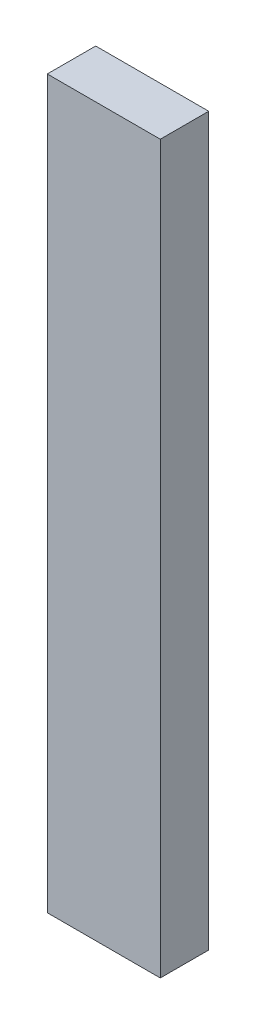
SolidWorks part; units mm, degrees
ref_plane "Front Plane" through (0, 0, 0) normal (1, 0, 0) x (0, 1, 0)
ref_plane "Top Plane" through (0, 0, 0) normal (0, 0, 1) x (0, 1, 0)
ref_plane "Right Plane" through (0, 0, 0) normal (0, 1, 0) x (-1, 0, 0)
sketch "Sketch1" plane through (0, 0, 0) normal (0, 0, 1) x (0, 1, 0)
  line L5 (0, 0) -> (57.15, 0)
  line L6 (0, 0) -> (0, 8.89)
  line L7 (0, 8.89) -> (57.15, 8.89)
  line L8 (57.15, 0) -> (57.15, 8.89)
  dimension "D1" = 8.89
  dimension "D2" = 57.15
extrude "Boss-Extrude1" add sketch "Sketch1" along normal blind 3.81
ref_plane "Plane1" through (-4.445, 0, 0) normal (1, 0, 0) x (0, 1, 0)
sketch "Sketch2" plane through (-4.445, 0, 0) normal (1, 0, 0) x (0, 1, 0)
  line L0 (5.2423, 8.1921) -> (5.2423, 3.81)
  line L1 (0, 3.81) -> (57.15, 3.81) construction
  line L2 (5.2423, 3.81) -> (0, 3.81)
  arc A0 (0, 3.81) -> (5.2423, 8.1921) centre (4.8122, 3.3799) cw
sketch "Sketch3" plane through (0, 0, 0) normal (0, -1, 0) x (1, 0, 0)
  line L1 (-8.89, 0) -> (-10.3809, 0)
  line L2 (-8.89, 0) -> (-8.89, 8.0093)
  line L3 (-8.89, 8.0093) -> (-10.3809, 8.0093)
  line L4 (-10.3809, 0) -> (-10.3809, 8.0093)
  line L5 (0, 0) -> (1.1414, 0)
  line L6 (0, 0) -> (0, 7.3991)
  line L7 (0, 7.3991) -> (1.1414, 7.3991)
  line L8 (1.1414, 0) -> (1.1414, 7.3991)
extrude "Cut-Extrude1" [suppressed] cut sketch "Sketch3" against normal through all
